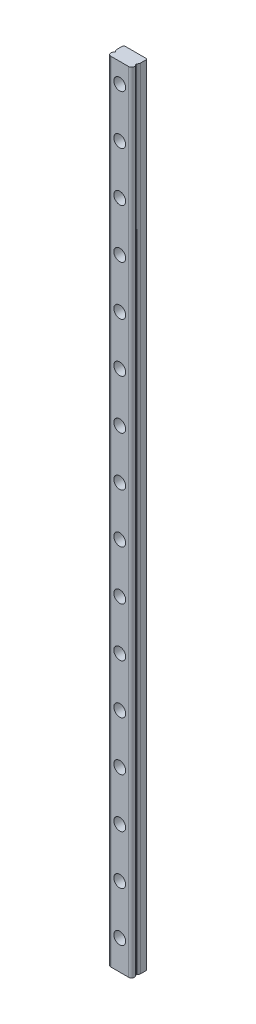
SolidWorks part; units mm, degrees
ref_plane "Front Plane" through (0, 0, 0) normal (0, 0, 1) x (1, 0, 0)
ref_plane "Top Plane" through (0, 0, 0) normal (0, 1, 0) x (1, 0, 0)
ref_plane "Right Plane" through (0, 0, 0) normal (1, 0, 0) x (0, 0, -1)
sketch "Sketch1" plane through (0, 0, 0) normal (0, 0, 1) x (1, 0, 0)
  line L1 (-6, 0) -> (6, 0)
  line L2 (-6, 0) -> (-6, 400)
  line L3 (-6, 400) -> (6, 400)
  line L4 (6, 0) -> (6, 400)
  dimension "D1" = 12
  dimension "D2" = 6
  dimension "D3" = 400
extrude "Boss-Extrude1" add sketch "Sketch1" along normal blind 8
sketch "Sketch2" plane through (0, 400, 0) normal (0, 1, 0) x (1, 0, 0)
  line L0 (-5.5, 0) -> (-6, -0.5)
  line L1 (6, 0) -> (-6, 0) construction
  line L2 (-6, -8) -> (-6, 0) construction
  line L3 (0, 0) -> (0, -8) construction
  line L4 (6, -8) -> (-6, -8) construction
  line L5 (-5.5, 0) -> (-7.7603, 0)
  line L6 (-7.7603, 0) -> (-7.7603, -8)
  line L7 (-7.7603, -8) -> (-4.5, -8)
  line L8 (-6, -0.5) -> (-6, -3.5)
  line L9 (6, -0.5) -> (6, -3.5)
  line L10 (7.7603, -8) -> (4.5, -8)
  line L11 (7.7603, 0) -> (7.7603, -8)
  line L12 (5.5, 0) -> (7.7603, 0)
  line L13 (5.5, 0) -> (6, -0.5)
  arc A0 (-5.4922, -5.375) -> (-4.5, -8) centre (-4.5, -6.5) ccw
  arc A1 (-6, -3.5) -> (-5.4922, -4.625) centre (-4.5, -3.5) ccw
  arc A2 (-5.4922, -4.625) -> (-5.4922, -5.375) centre (-5.8229, -5) cw
  arc A3 (5.4922, -4.625) -> (5.4922, -5.375) centre (5.8229, -5) ccw
  arc A4 (6, -3.5) -> (5.4922, -4.625) centre (4.5, -3.5) cw
  arc A5 (5.4922, -5.375) -> (4.5, -8) centre (4.5, -6.5) cw
  dimension "D3" = 3
  dimension "D4" = 3
  dimension "D5" = 0.5
  dimension "D1" = 0.5
  dimension "D2" = 0.5
extrude "Cut-Extrude1" cut sketch "Sketch2" against normal through all
sketch "Sketch3" plane through (0, 0, 8) normal (0, 0, 1) x (1, 0, 0)
  line L0 (4.5, 400) -> (-4.5, 400) construction
  circle A0 centre (0, 390) radius 3
  dimension "D1" = 6
  dimension "D2" = 10
extrude "Cut-Extrude2" cut sketch "Sketch3" against normal blind 4.5
sketch "Sketch4" plane through (0, 0, 3.5) normal (0, 0, 1) x (1, 0, 0)
  circle A0 centre (0, 390) radius 1.75
  dimension "D1" = 3.5
extrude "Cut-Extrude3" cut sketch "Sketch4" against normal through all
pattern_linear "LPattern1" count 16 spacing 25 along (0, -1, 0) of "Cut-Extrude2", "Cut-Extrude3"
